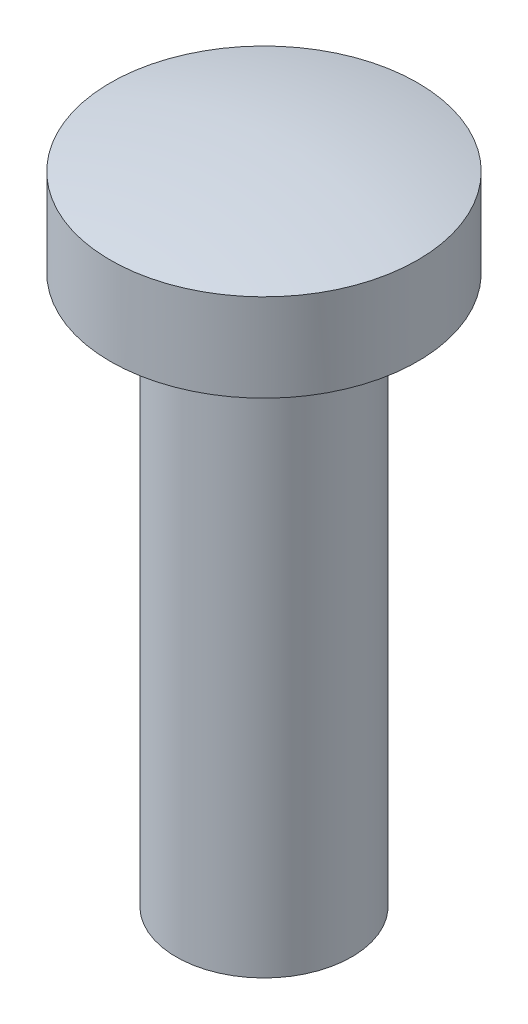
SolidWorks part; units mm, degrees
material "3.3537 (EN-AW 3535)"
ref_plane "Vorderansicht" through (0, 0, 0) normal (0, 0, 1) x (1, 0, 0)
ref_plane "Draufsicht" through (0, 0, 0) normal (0, 1, 0) x (1, 0, 0)
ref_plane "Seitenansicht" through (0, 0, 0) normal (1, 0, 0) x (0, 0, -1)
sketch "Skizze1" plane through (0, 0, 0) normal (0, 0, 1) x (1, 0, 0)
  line L0 (0, 0) -> (0, 27.8739) construction
  line L1 (0, 0) -> (0, 29.8329)
  line L4 (4, 25) -> (7, 25)
  line L5 (7, 29) -> (7, 25)
  line L7 (4, 25) -> (4, 0)
  line L8 (4, 0) -> (0, 0)
  arc A0 (7, 29) -> (0, 29.8329) centre (0, 0) ccw
  dimension "D1" = 3
  dimension "InnenDurchmesser" = 8
  dimension "D2" = 4
  dimension "Länge" = 25
revolve "Rotation1" add sketch "Skizze1" angle 360 about L1
other "PropertyManager"
